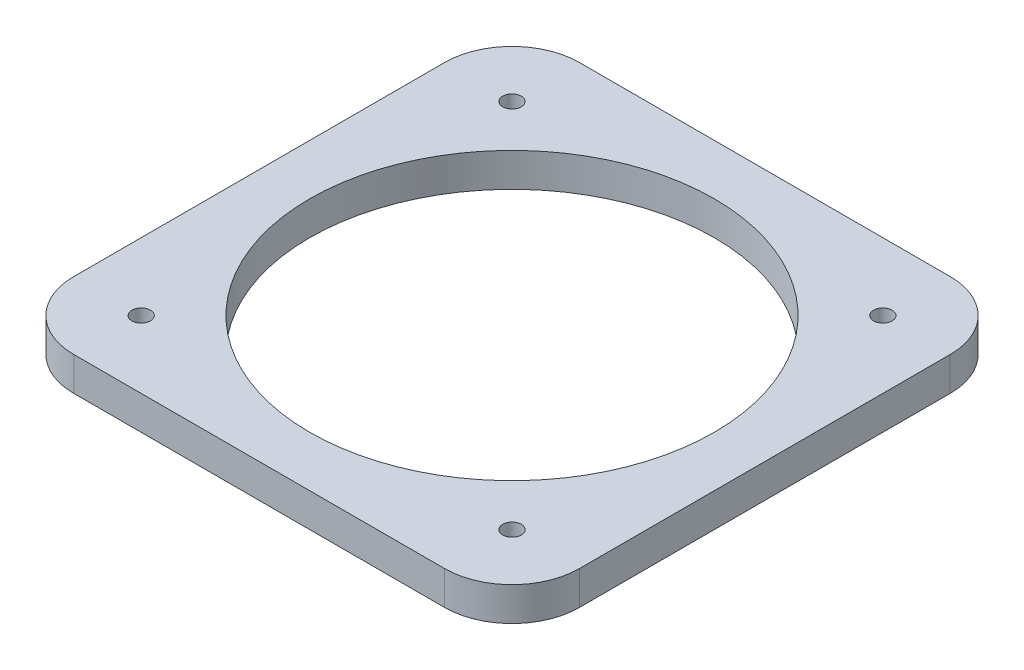
SolidWorks part; units mm, degrees
material "Acrylic (Medium-high impact)"
ref_plane "Front Plane" through (0, 0, 0) normal (0, 0, 1) x (1, 0, 0)
ref_plane "Top Plane" through (0, 0, 0) normal (0, 1, 0) x (1, 0, 0)
ref_plane "Right Plane" through (0, 0, 0) normal (1, 0, 0) x (0, 0, -1)
sketch "Sketch1" plane through (0, 0, 0) normal (0, 1, 0) x (1, 0, 0)
  line L1 (47.625, -47.625) -> (-47.625, -47.625)
  line L2 (47.625, -47.625) -> (47.625, 47.625)
  line L3 (47.625, 47.625) -> (-47.625, 47.625)
  line L4 (-47.625, -47.625) -> (-47.625, 47.625)
  line L5 (47.625, -47.625) -> (-47.625, 47.625) construction
  line L6 (47.625, 47.625) -> (-47.625, -47.625) construction
  circle A0 centre (0, 0) radius 38.1
  point P0 (0, 0)
  dimension "D1" = 76.2
  dimension "D3" = 95.25
extrude "Boss-Extrude1" add sketch "Sketch1" along normal blind 6.35
sketch "Sketch2" plane through (0, 6.35, 0) normal (0, 1, 0) x (1, 0, 0)
  line L1 (34.925, -34.925) -> (-34.925, -34.925) construction
  line L2 (34.925, -34.925) -> (34.925, 34.925) construction
  line L3 (34.925, 34.925) -> (-34.925, 34.925) construction
  line L4 (-34.925, -34.925) -> (-34.925, 34.925) construction
  line L5 (34.925, -34.925) -> (-34.925, 34.925) construction
  line L6 (34.925, 34.925) -> (-34.925, -34.925) construction
  circle A0 centre (-34.925, 34.925) radius 1.75
  point P0 (0, 0)
  dimension "D2" = 3.5
  dimension "D1" = 69.85
extrude "Cut-Extrude1" cut sketch "Sketch2" against normal through all
pattern_circular "CirPattern1" count 4 over 360 about axis through (0, 0, 0) along (0, 1, 0) of "Cut-Extrude1"
fillet "Fillet1" radius 12.7 4 edges at (-47.625, 3.175, -47.625) (-47.625, 3.175, 47.625) (47.625, 3.175, 47.625) (47.625, 3.175, -47.625)
